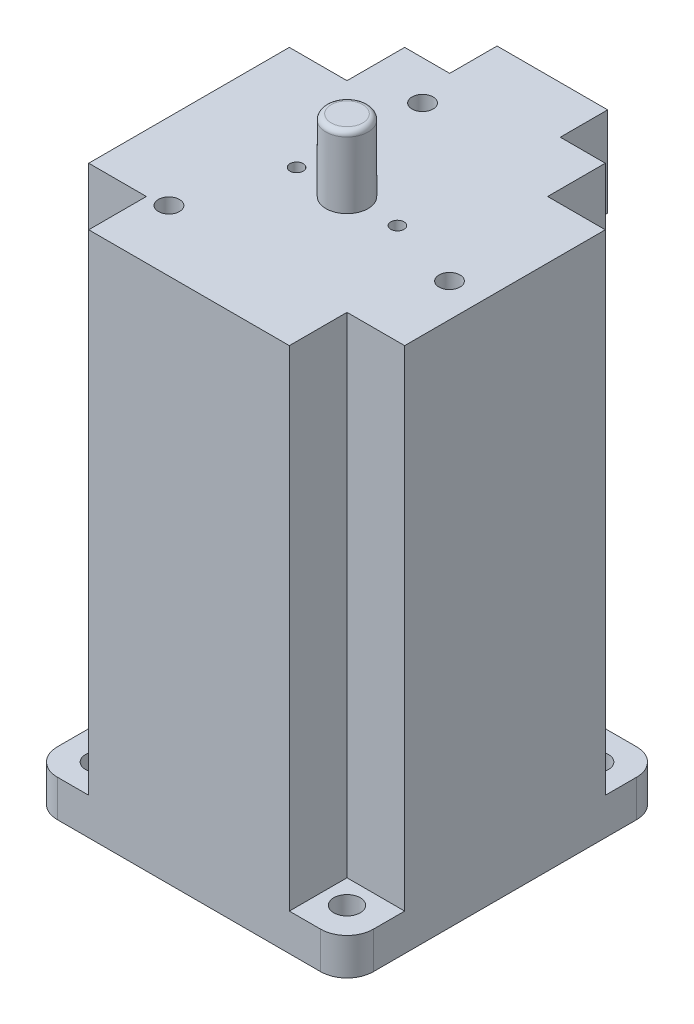
SolidWorks part; units mm, degrees
ref_plane "Front Plane" through (0, 0, 0) normal (0, 0, 1) x (1, 0, 0)
ref_plane "Top Plane" through (0, 0, 0) normal (0, 1, 0) x (1, 0, 0)
ref_plane "Right Plane" through (0, 0, 0) normal (1, 0, 0) x (0, 0, -1)
sketch "Sketch1" plane through (0, 0, 0) normal (0, 1, 0) x (1, 0, 0)
  line L1 (-30, 30) -> (30, 30)
  line L2 (-30, 30) -> (-30, -30)
  line L3 (-30, -30) -> (30, -30)
  line L4 (30, 30) -> (30, -30)
  line L5 (-30, 30) -> (30, -30) construction
  line L6 (-30, -30) -> (30, 30) construction
  point P0 (0, 0)
  dimension "D1" = 60
extrude "Boss-Extrude1" add sketch "Sketch1" along normal blind 100 contours L2 L1 L4 L3
sketch "Sketch2" plane through (0, 100, 0) normal (0, 1, 0) x (1, 0, 0)
  line L0 (-30, 30) -> (-30, 19.05)
  line L1 (-30, 30) -> (-30, -30) construction
  line L2 (-30, 19.05) -> (-19.05, 19.05)
  line L3 (-19.05, 19.05) -> (-19.05, 30)
  line L5 (-19.05, 30) -> (-30, 30)
  dimension "D1" = 10.95
  dimension "D2" = 10.95
  dimension "D3" = 10.95
  dimension "D4" = 10.95
extrude "Cut-Extrude1" cut sketch "Sketch2" against normal blind 93 contours L2 L3 L5 L0
mirror "Mirror1" about plane through (0, 0, 0) normal (1, 0, 0) of "Cut-Extrude1"
mirror "Mirror2" about plane through (0, 0, 0) normal (0, 0, 1) of "Mirror1", "Cut-Extrude1"
sketch "Sketch5" plane through (0, 0, 0) normal (0, -1, 0) x (1, 0, 0)
  line L0 (-30, 30) -> (30, 30) construction
  line L1 (-30, -30) -> (30, -30) construction
  line L3 (30, -30) -> (30, 30) construction
  circle A0 centre (-23.57, -23.57) radius 2.5
  circle A1 centre (23.57, -23.57) radius 2.5
  circle A2 centre (23.57, 23.57) radius 2.5
  circle A3 centre (-23.57, 23.57) radius 2.5
  dimension "D1" = 5
  dimension "D2" = 5
  dimension "D3" = 5
  dimension "D4" = 5
  dimension "D5" = 47.14
  dimension "D6" = 6.43
  dimension "D7" = 6.43
  dimension "D8" = 47.14
  dimension "D9" = 47.14
  dimension "D10" = 6.43
  dimension "D11" = 47.14
  dimension "D12" = 6.43
sketch "Sketch6" plane through (0, 0, 0) normal (0, -1, 0) x (1, 0, 0)
extrude "Cut-Extrude2" cut sketch "Sketch5" against normal blind 93 contours A1 | A0 | A2 | A3
sketch "Sketch7" plane through (0, 0, 0) normal (0, -1, 0) x (1, 0, 0)
  circle A0 centre (0, 0) radius 19.05
  dimension "D1" = 38.1
extrude "Boss-Extrude4" add sketch "Sketch7" along normal blind 1.8 contours A0
sketch "Sketch8" plane through (0, -1.8, 0) normal (0, -1, 0) x (1, 0, 0)
  circle A0 centre (0, 0) radius 4
  dimension "D1" = 8
extrude "Boss-Extrude5" add sketch "Sketch8" along normal blind 20.4
fillet "Fillet2" radius 5 4 edges at (-30, 3.5, -30) (30, 3.5, -30) (30, 3.5, 30) (-30, 3.5, 30)
sketch "Sketch15" plane through (0, 100, 0) normal (0, 1, 0) x (1, 0, 0)
  circle A0 centre (0, 0) radius 4
  dimension "D1" = 8
extrude "Boss-Extrude6" add sketch "Sketch15" along normal blind 13.6 contours A0
fillet "Fillet4" radius 1 1 edges at (0, 113.6, 4)
sketch "Sketch16" plane through (0, 0, 0) normal (1, 0, 0) x (0, 0, -1)
sketch "Sketch17" plane through (0, -22.2, 0) normal (0, -1, 0) x (1, 0, 0)
  line L0 (-2.5528, -3.1) -> (2.5528, -3.1)
  arc A1 (-2.5528, -3.1) -> (2.5528, -3.1) centre (0, 0) ccw
extrude "Cut-Extrude4" cut sketch "Sketch17" against normal blind 15.5 contours L0 A1
sketch "Sketch20" plane through (0, 0, -30) normal (0, 0, -1) x (-1, 0, 0)
  line L1 (19.05, 100) -> (-19.05, 100) construction
  line L2 (0, 100) -> (10.5, 100)
  line L3 (10.5, 100) -> (10.5, 83)
  line L4 (10.5, 83) -> (-10.5, 83)
  line L5 (-10.5, 83) -> (-10.5, 100)
  line L6 (-10.5, 100) -> (0, 100)
  dimension "D1" = 10.5
  dimension "D2" = 17
  dimension "D3" = 21
extrude "Boss-Extrude7" add sketch "Sketch20" along normal blind 9
sketch "Sketch21" plane through (0, 83, 0) normal (0, -1, 0) x (1, 0, 0)
  line L0 (0, -39) -> (-6, -39)
  line L1 (10.5, -39) -> (-10.5, -39) construction
  line L2 (-6, -39) -> (-6, -34)
  line L3 (-6, -34) -> (6, -34)
  line L4 (6, -34) -> (6, -39)
  line L5 (6, -39) -> (0, -39)
  dimension "D1" = 6
  dimension "D2" = 5
  dimension "D3" = 12
extrude "Boss-Extrude8" add sketch "Sketch21" along normal blind 9
sketch "Sketch22" plane through (0, 100, 0) normal (0, 1, 0) x (1, 0, 0)
  line L0 (0, -30) -> (0, 39)
  line L1 (-19.05, -30) -> (19.05, -30) construction
  line L2 (-10.5, 39) -> (10.5, 39) construction
  line L3 (-30, 0) -> (30, 0)
  line L4 (-30, 19.05) -> (-30, -19.05) construction
  line L5 (30, 19.05) -> (30, -19.05) construction
  line L6 (0, 0) -> (-9.575, 0)
  line L7 (0, 0) -> (9.575, 0)
  circle A0 centre (-9.575, 0) radius 1.25
  circle A1 centre (9.575, 0) radius 1.25
  arc A2 (-10.0577, 21.7909) -> (-16.9041, -17.0368) centre (0, 0) ccw
  circle A3 centre (-8.2085, 22.5526) radius 2
  circle A4 centre (-15.4269, -18.3851) radius 2
  circle A5 centre (23.6354, -4.1676) radius 2
  arc A6 (-13.8426, -19.6057) -> (23.2063, -6.121) centre (0, 0) ccw
  arc A7 (23.9003, -2.1852) -> (-6.3022, 23.1578) centre (0, 0) ccw
  dimension "D3" = 2.5
  dimension "D4" = 2.5
  dimension "D5" = 48
  dimension "D7" = 4
  dimension "D10" = 4
  dimension "D11" = 4
  dimension "D1" = 9.575
  dimension "D2" = 9.575
extrude "Cut-Extrude7" cut sketch "Sketch22" against normal blind 4 contours A3 | A4 | A5 | A1 | A0
sketch "Sketch26" plane through (0, 100, 0) normal (0, 1, 0) x (1, 0, 0)
  line L0 (-10.5, 30) -> (10.5, 30)
